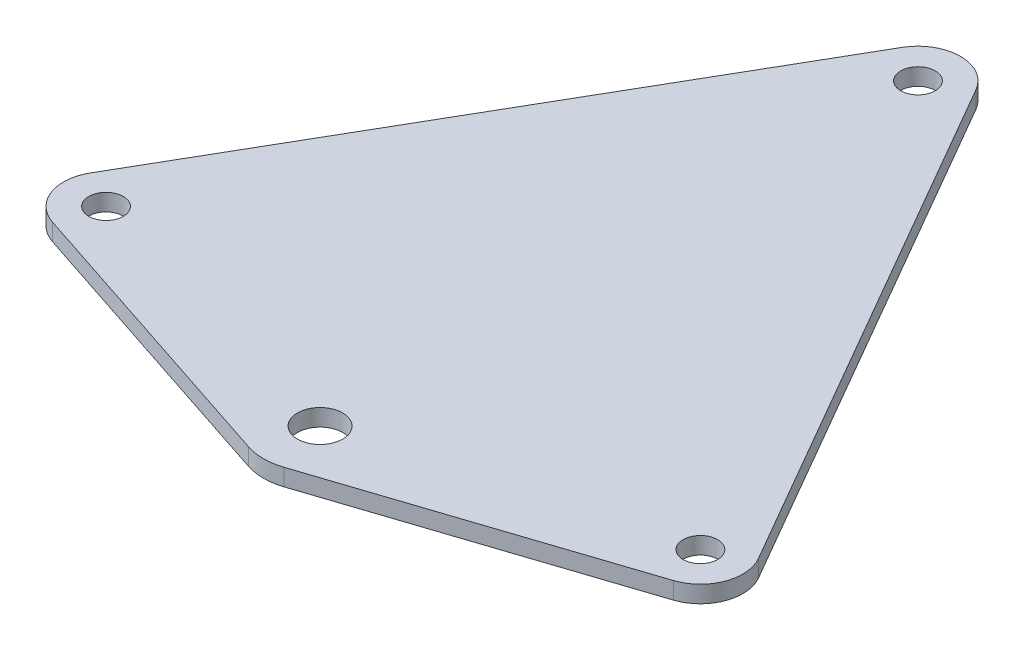
SolidWorks part; units mm, degrees
ref_plane "Front Plane" through (0, 0, 0) normal (0, 0, 1) x (1, 0, 0)
ref_plane "Top Plane" through (0, 0, 0) normal (0, 1, 0) x (1, 0, 0)
ref_plane "Right Plane" through (0, 0, 0) normal (1, 0, 0) x (0, 0, -1)
sketch "Sketch1" plane through (0, 0, 0) normal (0, 1, 0) x (1, 0, 0)
  line L0 (0, 60.6218) -> (-52.5, -30.3109) construction
  line L1 (-52.5, -30.3109) -> (52.5, -30.3109) construction
  line L2 (52.5, -30.3109) -> (0, 60.6218) construction
  line L3 (-6.4952, 64.3718) -> (-58.9952, -26.5609)
  line L4 (-52.5, -37.8109) -> (52.5, -37.8109)
  line L5 (6.4952, 64.3718) -> (58.9952, -26.5609)
  line L6 (0, 60.6218) -> (0, 0) construction
  line L7 (0, 0) -> (-52.5, -30.3109) construction
  line L8 (0, 0) -> (52.5, -30.3109) construction
  line L9 (0, 0) -> (0, -45) construction
  line L10 (-54.8499, -37.4332) -> (-3.1332, -54.4965)
  line L11 (3.1332, -54.4965) -> (54.8499, -37.4332)
  line L12 (-19.1038, 57.533) -> (-6.1134, 50.033) construction
  line L13 (-40.2731, -45.3109) -> (-40.2731, -30.3109) construction
  line L14 (-40.2731, -45.3109) -> (0, 60.6218) construction
  line L15 (-83.9292, -28.0025) -> (-44.1287, 76.6871) construction
  line L16 (0, 0) -> (-64.0289, 24.3423) construction
  line L17 (-83.9292, -28.0025) -> (-41.6013, -44.0946) construction
  line L18 (-44.1287, 76.6871) -> (-1.8007, 60.595) construction
  circle A0 centre (0, 60.6218) radius 7.5 construction
  circle A1 centre (52.5, -30.3109) radius 7.5 construction
  circle A2 centre (-52.5, -30.3109) radius 7.5 construction
  arc A3 (-52.5, -37.8109) -> (-58.9952, -26.5609) centre (-52.5, -30.3109) cw
  arc A4 (58.9952, -26.5609) -> (52.5, -37.8109) centre (52.5, -30.3109) cw
  arc A5 (6.4952, 64.3718) -> (-6.4952, 64.3718) centre (0, 60.6218) ccw
  circle A6 centre (0, 60.6218) radius 3.05
  circle A7 centre (52.5, -30.3109) radius 3.05
  circle A8 centre (-52.5, -30.3109) radius 3.05
  circle A9 centre (0, -45) radius 10 construction
  arc A10 (-3.1332, -54.4965) -> (3.1332, -54.4965) centre (0, -45) ccw
  circle A11 centre (0, -45) radius 4
  arc A12 (0, 60.6218) -> (-29.9926, -52.6825) centre (0, 0) ccw construction
  circle A13 centre (-19.1038, 57.533) radius 6 construction
  circle A14 centre (-40.2731, -45.3109) radius 6 construction
  point P33 (-20.1366, 7.6554)
  dimension "D2" = 15
  dimension "D3" = 6.1
  dimension "D4" = 20
  dimension "D6" = 8
  dimension "D7" = 12
  dimension "D1" = 105
  dimension "D5" = 45
  dimension "D8" = 15
  dimension "D9" = 112
  dimension "D10" = 68.5
extrude "Boss-Extrude1" add sketch "Sketch1" along normal blind 3 contours L5 A5 L3 A3 L4 A4 A8 A7 A6 | L10 A10 L11 A4 L4 A3 A11
